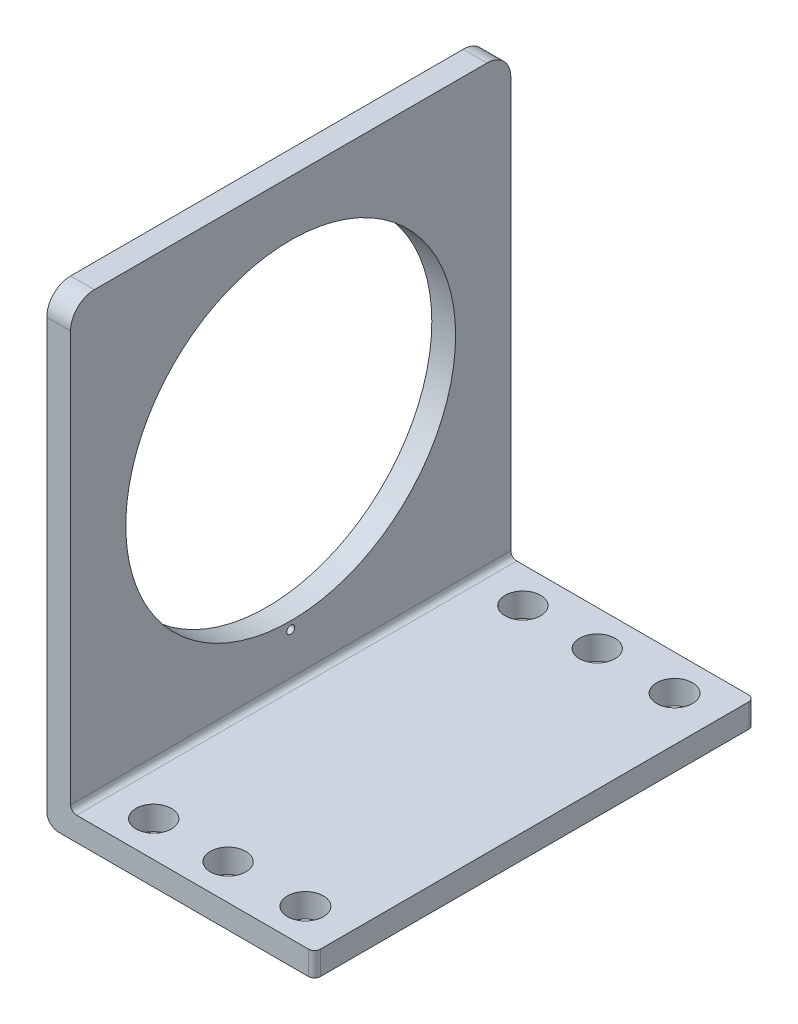
SolidWorks part; units mm, degrees
ref_plane "Front Plane" through (0, 0, 0) normal (0, 0, 1) x (1, 0, 0)
ref_plane "Top Plane" through (0, 0, 0) normal (0, 1, 0) x (1, 0, 0)
ref_plane "Right Plane" through (0, 0, 0) normal (1, 0, 0) x (0, 0, -1)
sketch "Sketch1" plane through (0, 0, 0) normal (0, 0, 1) x (1, 0, 0)
  line L0 (0, 0) -> (0, 37)
  line L1 (-2, 37) -> (-2, -1)
  line L2 (-1, -2) -> (20.5, -2)
  line L3 (20.5, 0) -> (0, 0)
  line L4 (-2, 37) -> (0, 37)
  line L5 (20.5, -2) -> (20.5, 0)
  arc A0 (-2, -1) -> (-1, -2) centre (-1, -1) ccw
  point P9 (-2, -2)
  dimension "D1" = 2
  dimension "D4" = 1
  dimension "D2" = 22.5
  dimension "D3" = 39
  dimension "D5" = 2
extrude "Boss-Extrude1" add sketch "Sketch1" along normal blind 37 contours L0 L4 L1 A0 L2 L5 L3
sketch "Sketch2" plane through (0, 0, 0) normal (1, 0, 0) x (0, 0, -1)
  line L0 (-18.5, 37) -> (-18.5, 0) construction
  line L1 (-37, 37) -> (0, 37) construction
  line L2 (-37, 0) -> (0, 0) construction
  line L4 (0, 0) -> (0, 37) construction
  line L5 (0, 18.5) -> (-37, 18.5) construction
  line L6 (-37, 0) -> (-37, 37) construction
  circle A0 centre (-18.5, 18.5) radius 13.8601
  circle A1 centre (-18.5, 4) radius 0.3327
  point P16 (0, 0)
  dimension "D1" = 4
extrude "Cut-Extrude1" cut sketch "Sketch2" against normal blind 10
sketch "Sketch3" plane through (0, 0, 0) normal (0, 1, 0) x (1, 0, 0)
  line L0 (10.25, 0) -> (10.25, -37) construction
  line L1 (20.5, 0) -> (0, 0) construction
  line L2 (20.5, -37) -> (0, -37) construction
  line L4 (20.5, -18.5) -> (0, -18.5) construction
  line L5 (20.5, -37) -> (20.5, 0) construction
  line L6 (0, -37) -> (0, 0) construction
  circle A0 centre (16.75, -2.987) radius 1.5138
  circle A1 centre (10.25, -2.987) radius 1.4952
  circle A2 centre (4, -2.987) radius 1.4952
  circle A3 centre (16.75, -34.013) radius 1.5138
  circle A4 centre (10.25, -34.013) radius 1.4952
  circle A5 centre (4, -34.013) radius 1.4952
  dimension "D2" = 6.5
extrude "Cut-Extrude2" cut sketch "Sketch3" against normal blind 10
fillet "Fillet1" radius 2 2 edges at (-1, 37, 0) (-1, 37, 37)
fillet "Fillet2" radius 0.5 1 edges at (0, 0, 18.5)
fillet "Fillet3" radius 0.5 2 edges at (20.5, -1, 0) (20.5, -1, 37)
